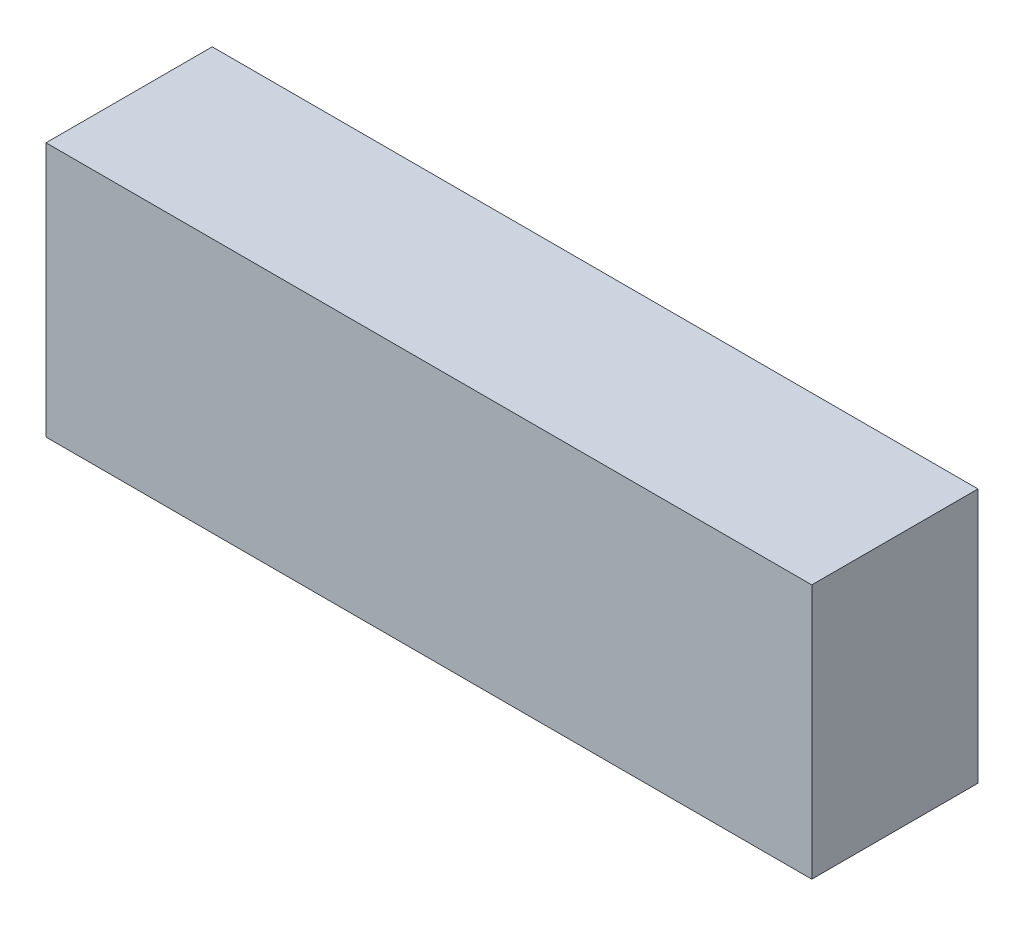
SolidWorks part; units mm, degrees
ref_plane "Front Plane" through (0, 0, 0) normal (0, 0, 1) x (1, 0, 0)
ref_plane "Top Plane" through (0, 0, 0) normal (0, 1, 0) x (1, 0, 0)
ref_plane "Right Plane" through (0, 0, 0) normal (1, 0, 0) x (0, 0, -1)
sketch "Sketch1" plane through (0, 0, 0) normal (0, 0, 1) x (1, 0, 0)
  line L1 (-43.8785, 14.605) -> (43.8785, 14.605)
  line L2 (-43.8785, 14.605) -> (-43.8785, -14.605)
  line L3 (-43.8785, -14.605) -> (43.8785, -14.605)
  line L4 (43.8785, 14.605) -> (43.8785, -14.605)
  line L5 (-43.8785, 14.605) -> (43.8785, -14.605) construction
  line L6 (-43.8785, -14.605) -> (43.8785, 14.605) construction
  point P0 (0, 0)
  dimension "D1" = 29.21
  dimension "D2" = 87.757
extrude "Boss-Extrude1" add sketch "Sketch1" along normal blind 19.05
